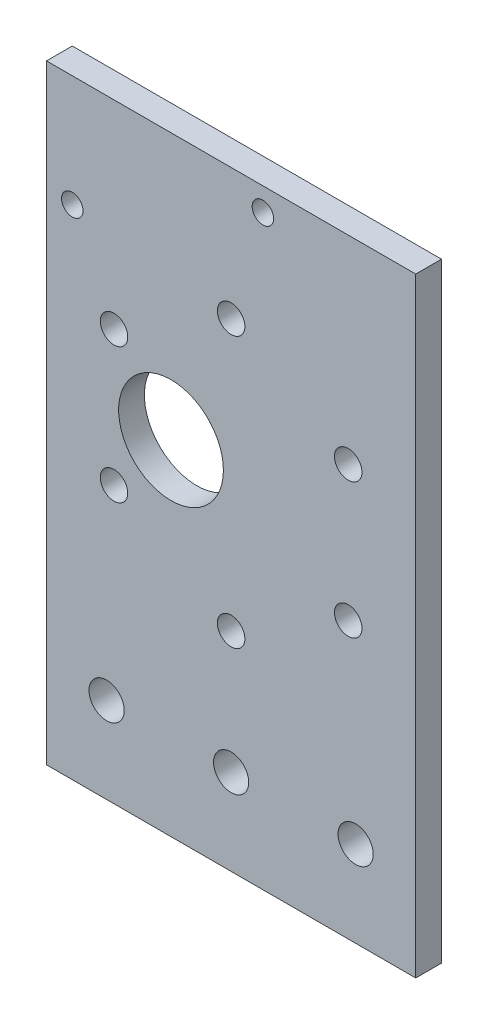
SolidWorks part; units mm, degrees
ref_plane "正面" through (0, 0, 0) normal (0, 0, 1) x (1, 0, 0)
ref_plane "平面" through (0, 0, 0) normal (0, 1, 0) x (1, 0, 0)
ref_plane "右側面" through (0, 0, 0) normal (1, 0, 0) x (0, 0, -1)
sketch "ｽｹｯﾁ1" plane through (0, 0, 0) normal (0, 0, 1) x (1, 0, 0)
  line L1 (-20, 14.5) -> (20, 14.5)
  line L2 (-20, 14.5) -> (-20, -14.5)
  line L3 (-20, -14.5) -> (20, -14.5)
  line L4 (20, 14.5) -> (20, -14.5)
  line L5 (-20, 14.5) -> (20, -14.5) construction
  line L6 (-20, -14.5) -> (20, 14.5) construction
  point P0 (0, 0)
  dimension "D1" = 40
  dimension "D2" = 29
extrude "ﾎﾞｽ - 押し出し1" add sketch "ｽｹｯﾁ1" along normal blind 3
sketch "ｽｹｯﾁ2" plane through (0, 0, 3) normal (0, 0, 1) x (1, 0, 0)
  line L1 (-20, 14.5) -> (-16.5, 14.5)
  line L2 (-20, 14.5) -> (-20, 10.5)
  line L3 (-20, 10.5) -> (-16.5, 10.5)
  line L4 (-16.5, 14.5) -> (-16.5, 10.5)
  line L5 (-20, -14.5) -> (-16.5, -14.5)
  line L6 (-20, -14.5) -> (-20, -10.5)
  line L7 (-20, -10.5) -> (-16.5, -10.5)
  line L8 (-16.5, -14.5) -> (-16.5, -10.5)
  line L9 (20, -14.5) -> (16.5, -14.5)
  line L10 (20, -14.5) -> (20, -10.5)
  line L11 (20, -10.5) -> (16.5, -10.5)
  line L12 (16.5, -14.5) -> (16.5, -10.5)
  line L13 (20, 14.5) -> (16.5, 14.5)
  line L14 (20, 14.5) -> (20, 10.5)
  line L15 (20, 10.5) -> (16.5, 10.5)
  line L16 (16.5, 14.5) -> (16.5, 10.5)
  circle A0 centre (-16.5, 10.5) radius 2.1
  circle A1 centre (-16.5, -10.5) radius 2.1
  circle A2 centre (16.5, -10.5) radius 2.1
  circle A3 centre (16.5, 10.5) radius 2.1
  dimension "D9" = 4.2
  dimension "D10" = 4.2
  dimension "D11" = 4.2
  dimension "D12" = 4.2
  dimension "D1" = 3.5
  dimension "D2" = 4
  dimension "D3" = 3.5
  dimension "D4" = 4
  dimension "D5" = 3.5
  dimension "D6" = 4
  dimension "D7" = 3.5
  dimension "D8" = 4
extrude "ｶｯﾄ - 押し出し1" cut sketch "ｽｹｯﾁ2" against normal blind 3 contours L3 A0 L4 | L4 A0 L3 | L8 A1 L7 | L7 A1 L8 | L12 A2 L11 | L11 A2 L12 | L16 A3 L15 | L15 A3 L16
sketch "ｽｹｯﾁ3" plane through (0, -14.5, 0) normal (0, -1, 0) x (1, 0, 0)
  line L1 (20, 0) -> (-20, 0)
  line L2 (20, 0) -> (20, 3)
  line L3 (20, 3) -> (-20, 3)
  line L4 (-20, 0) -> (-20, 3)
extrude "ﾎﾞｽ - 押し出し2" add sketch "ｽｹｯﾁ3" along normal blind 10
sketch "ｽｹｯﾁ4" plane through (0, 14.5, 0) normal (0, 1, 0) x (1, 0, 0)
  line L1 (20, -3) -> (-20, -3)
  line L2 (20, -3) -> (20, 0)
  line L3 (20, 0) -> (-20, 0)
  line L4 (-20, -3) -> (-20, 0)
extrude "ﾎﾞｽ - 押し出し3" add sketch "ｽｹｯﾁ4" along normal blind 10
sketch "ｽｹｯﾁ6" plane through (20, 0, 0) normal (1, 0, 0) x (0, 0, -1)
  line L1 (0, 24.5) -> (-3, 24.5)
  line L2 (0, 24.5) -> (0, -24.5)
  line L3 (0, -24.5) -> (-3, -24.5)
  line L4 (-3, 24.5) -> (-3, -24.5)
extrude "ﾎﾞｽ - 押し出し5" add sketch "ｽｹｯﾁ6" along normal blind 42
sketch "ｽｹｯﾁ7" plane through (0, 0, 3) normal (0, 0, 1) x (1, 0, 0)
  line L0 (62, 0) -> (43.1058, 0)
  line L1 (62, 24.5) -> (62, -24.5) construction
  line L2 (43.1058, 0) -> (36.1058, 0)
  line L7 (31.9689, -11.1369) -> (54.2427, 11.1369) construction
  line L8 (31.9689, 11.1369) -> (54.2427, -11.1369) construction
  line L9 (43.1058, 0) -> (29.4659, 7.875)
  line L10 (43.1058, 0) -> (43.1058, 15.75)
  line L11 (43.1058, 0) -> (56.7457, 7.875)
  line L12 (43.1058, 0) -> (29.4659, -7.875)
  line L13 (43.1058, 0) -> (43.1058, -15.75)
  line L14 (43.1058, 0) -> (56.7457, -7.875)
  circle A0 centre (43.1058, 0) radius 15.75
  circle A5 centre (29.4659, 7.875) radius 1.75
  circle A6 centre (43.1058, 15.75) radius 1.75
  circle A7 centre (29.4659, -7.875) radius 1.75
  circle A8 centre (43.1058, -15.75) radius 1.75
  circle A9 centre (56.7457, -7.875) radius 1.75
  circle A10 centre (56.7457, 7.875) radius 1.75
  circle A11 centre (36.1058, 0) radius 6.1
  dimension "D3" = 60
  dimension "D4" = 7
  dimension "D5" = 60
  dimension "D6" = 60
  dimension "D7" = 31.5
  dimension "D8" = 3.5
  dimension "D9" = 3.5
  dimension "D10" = 3.5
  dimension "D11" = 3.5
  dimension "D12" = 3.5
  dimension "D13" = 3.5
  dimension "D14" = 12.2
  dimension "D2" = 60
  dimension "D15" = 18.8942
sketch "ｽｹｯﾁ8" plane through (-20, 0, 0) normal (-1, 0, 0) x (0, 0, 1)
  line L1 (3, -24.5) -> (0, -24.5)
  line L2 (3, -24.5) -> (3, 24.5)
  line L3 (3, 24.5) -> (0, 24.5)
  line L4 (0, -24.5) -> (0, 24.5)
extrude "ﾎﾞｽ - 押し出し6" add sketch "ｽｹｯﾁ8" along normal blind 2
sketch "ｽｹｯﾁ9" plane through (62, 0, 0) normal (1, 0, 0) x (0, 0, -1)
  line L1 (0, 24.5) -> (-3, 24.5)
  line L2 (0, 24.5) -> (0, -24.5)
  line L3 (0, -24.5) -> (-3, -24.5)
  line L4 (-3, 24.5) -> (-3, -24.5)
extrude "ﾎﾞｽ - 押し出し7" add sketch "ｽｹｯﾁ9" along normal blind 2
sketch "ｽｹｯﾁ10" plane through (0, -24.5, 0) normal (0, -1, 0) x (1, 0, 0)
  line L1 (-22, 0) -> (64, 0)
  line L2 (-22, 0) -> (-22, 3)
  line L3 (-22, 3) -> (64, 3)
  line L4 (64, 0) -> (64, 3)
extrude "ﾎﾞｽ - 押し出し8" add sketch "ｽｹｯﾁ10" along normal blind 10
sketch "ｽｹｯﾁ11" plane through (0, 24.5, 0) normal (0, 1, 0) x (1, 0, 0)
  line L1 (-22, 0) -> (64, 0)
  line L2 (-22, 0) -> (-22, -3)
  line L3 (-22, -3) -> (64, -3)
  line L4 (64, 0) -> (64, -3)
extrude "ﾎﾞｽ - 押し出し9" add sketch "ｽｹｯﾁ11" along normal blind 10
sketch "ｽｹｯﾁ12" plane through (0, 0, 3) normal (0, 0, 1) x (1, 0, 0)
  line L0 (64, -34.5) -> (64, -27)
  line L1 (64, 34.5) -> (64, -34.5) construction
  line L2 (64, 34.5) -> (64, 27)
  line L3 (64, -27) -> (54, -27)
  line L4 (64, 27) -> (54, 27)
  line L5 (-22, -34.5) -> (-22, -27)
  line L6 (-22, -34.5) -> (-22, 34.5) construction
  line L7 (-22, 34.5) -> (-22, 27)
  line L8 (-22, -27) -> (-12, -27)
  line L9 (-22, 27) -> (-12, 27)
  circle A0 centre (54, -27) radius 2.2
  circle A1 centre (54, 27) radius 2.2
  circle A2 centre (-12, -27) radius 2.2
  circle A3 centre (-12, 27) radius 2.2
  dimension "D4" = 4.4
  dimension "D5" = 4.4
  dimension "D11" = 4.4
  dimension "D12" = 4.4
  dimension "D1" = 7.5
  dimension "D2" = 7.5
  dimension "D3" = 10
  dimension "D6" = 10
  dimension "D7" = 7.5
  dimension "D8" = 7.5
  dimension "D9" = 10
  dimension "D10" = 10
sketch "ｽｹｯﾁ14" plane through (-22, 0, 0) normal (-1, 0, 0) x (0, 0, 1)
  line L0 (0, 34.5) -> (0, -34.5) construction
  line L1 (3, -34.5) -> (0, -34.5)
  line L2 (3, -34.5) -> (3, 34.5)
  line L3 (3, 34.5) -> (0, 34.5)
  line L4 (0, -34.5) -> (0, 34.5)
  line L5 (0, 34.5) -> (3, 34.5) construction
extrude "ｶｯﾄ - 押し出し5" cut sketch "ｽｹｯﾁ14" against normal blind 43
sketch "ｽｹｯﾁ17" plane through (0, -34.5, 0) normal (0, -1, 0) x (1, 0, 0)
  line L1 (21, 3) -> (64, 3)
  line L2 (21, 3) -> (21, 0)
  line L3 (21, 0) -> (64, 0)
  line L4 (64, 3) -> (64, 0)
extrude "ﾎﾞｽ - 押し出し10" add sketch "ｽｹｯﾁ17" along normal blind 20
sketch "ｽｹｯﾁ18" plane through (0, 0, 3) normal (0, 0, 1) x (1, 0, 0)
  line L0 (21, -54.5) -> (21, -34.5)
  line L1 (21, -54.5) -> (21, 34.5) construction
  line L3 (64, -54.5) -> (64, -34.5)
  line L4 (64, 34.5) -> (64, -54.5) construction
  line L5 (64, -34.5) -> (57, -34.5)
  line L6 (21, -34.5) -> (28, -34.5)
  circle A0 centre (28, -34.5) radius 2.05
  circle A1 centre (57, -34.5) radius 2.05
  dimension "D5" = 4.1
  dimension "D6" = 4.1
  dimension "D1" = 20
  dimension "D2" = 20
  dimension "D3" = 7
  dimension "D4" = 7
extrude "ｶｯﾄ - 押し出し6" cut sketch "ｽｹｯﾁ18" against normal blind 10
sketch "ｽｹｯﾁ19" plane through (0, 0, 3) normal (0, 0, 1) x (1, 0, 0)
  line L0 (42.5, -54.5) -> (42.5, 34.5)
  line L1 (64, -54.5) -> (21, -54.5) construction
  line L2 (21, 34.5) -> (64, 34.5) construction
  circle A0 centre (28, -34.5) radius 2.05 construction
  circle A1 centre (57, -34.5) radius 2.05 construction
  dimension "D2" = 14.5
  dimension "D1" = 14.5
sketch "ｽｹｯﾁ20" plane through (0, -54.5, 0) normal (0, -1, 0) x (1, 0, 0)
  line L1 (64, 0) -> (21, 0)
  line L2 (64, 0) -> (64, 3)
  line L3 (64, 3) -> (21, 3)
  line L4 (21, 0) -> (21, 3)
extrude "ﾎﾞｽ - 押し出し11" add sketch "ｽｹｯﾁ20" along normal blind 10
sketch "ｽｹｯﾁ21" plane through (0, 34.5, 0) normal (0, 1, 0) x (1, 0, 0)
  line L1 (64, 0) -> (21, 0)
  line L2 (64, 0) -> (64, -3)
  line L3 (64, -3) -> (21, -3)
  line L4 (21, 0) -> (21, -3)
extrude "ｶｯﾄ - 押し出し7" cut sketch "ｽｹｯﾁ21" against normal blind 10
sketch "ｽｹｯﾁ22" plane through (0, 0, 3) normal (0, 0, 1) x (1, 0, 0)
  line L0 (28, -34.5) -> (28, -54.5)
  line L1 (57, -34.5) -> (57, -54.5)
  circle A0 centre (28, -54.5) radius 2.2
  circle A1 centre (57, -54.5) radius 2.2
  dimension "D2" = 4.4
  dimension "D4" = 4.4
  dimension "D1" = 20
  dimension "D3" = 20
sketch "ｽｹｯﾁ23" plane through (0, 0, 3) normal (0, 0, 1) x (1, 0, 0)
  line L0 (21, 24.5) -> (21, 22.0635)
  line L1 (21, -64.5) -> (21, 24.5) construction
  line L2 (21, 22.0635) -> (24.0484, 22.0635)
  line L3 (24.0484, 22.0635) -> (24.0484, 11.7635)
  line L4 (24.0484, 11.7635) -> (46.2484, 11.7635)
  dimension "D1" = 10.3
  dimension "D2" = 22.2
sketch "ｽｹｯﾁ24" plane through (0, 24.5, 0) normal (0, 1, 0) x (1, 0, 0)
  line L1 (21, 0) -> (64, 0)
  line L2 (21, 0) -> (21, -3)
  line L3 (21, -3) -> (64, -3)
  line L4 (64, 0) -> (64, -3)
extrude "ﾎﾞｽ - 押し出し12" add sketch "ｽｹｯﾁ24" along normal blind 10
sketch "ｽｹｯﾁ25" plane through (0, 0, 3) normal (0, 0, 1) x (1, 0, 0)
  line L0 (21, 34.5) -> (21, 31.5)
  line L1 (21, -64.5) -> (21, 34.5) construction
  line L2 (21, 31.5) -> (24, 31.5)
  line L3 (24, 31.5) -> (24, 13.5)
  line L4 (24, 13.5) -> (46.2, 13.5)
  line L5 (46.2, 13.5) -> (46.2, 23.8)
  circle A0 centre (24, 13.5) radius 1.55
  circle A1 centre (46.2, 23.8) radius 1.55
  dimension "D6" = 3.1
  dimension "D7" = 3.1
  dimension "D1" = 3
  dimension "D2" = 3
  dimension "D3" = 18
  dimension "D4" = 22.2
  dimension "D5" = 10.3
sketch "ｽｹｯﾁ28" plane through (0, 0, 3) normal (0, 0, 1) x (1, 0, 0)
  line L0 (64, 34.5) -> (42.5, 34.5)
  line L1 (21, 34.5) -> (64, 34.5) construction
  line L2 (42.5, 34.5) -> (42.5, -4.5)
  line L3 (42.5, -4.5) -> (35.5, -4.5)
  line L4 (42.5, -4.5) -> (28.8601, 3.375)
  line L5 (42.5, -4.5) -> (56.1399, 3.375)
  line L6 (42.5, -4.5) -> (56.1399, -12.375)
  line L7 (42.5, -4.5) -> (42.5, -20.25)
  line L8 (42.5, -4.5) -> (28.8601, -12.375)
  circle A0 centre (42.5, -4.5) radius 15.75
  circle A1 centre (35.5, -4.5) radius 6.1
  circle A2 centre (42.5, 11.25) radius 1.6
  circle A3 centre (28.8601, -12.375) radius 1.6
  circle A4 centre (28.8601, 3.375) radius 1.6
  circle A5 centre (56.1399, 3.375) radius 1.6
  circle A6 centre (56.1399, -12.375) radius 1.6
  circle A7 centre (42.5, -20.25) radius 1.6
  dimension "D2" = 31.5
  dimension "D4" = 12.2
  dimension "D9" = 3.2
  dimension "D10" = 3.2
  dimension "D11" = 3.2
  dimension "D12" = 3.2
  dimension "D13" = 3.2
  dimension "D14" = 3.2
  dimension "D1" = 21.5
  dimension "D3" = 7
  dimension "D5" = 60
  dimension "D6" = 60
  dimension "D7" = 60
  dimension "D8" = 60
  dimension "D15" = 39
extrude "ｶｯﾄ - 押し出し9" cut sketch "ｽｹｯﾁ28" against normal blind 10
sketch "ｽｹｯﾁ29" plane through (0, -64.5, 0) normal (0, -1, 0) x (-1, 0, 0)
  line L1 (-21, 0) -> (-64, 0)
  line L2 (-21, 0) -> (-21, -3)
  line L3 (-21, -3) -> (-64, -3)
  line L4 (-64, 0) -> (-64, -3)
extrude "ｶｯﾄ - 押し出し10" cut sketch "ｽｹｯﾁ29" against normal blind 20
sketch "ｽｹｯﾁ30" plane through (0, 0, 3) normal (0, 0, 1) x (1, 0, 0)
  line L1 (64, -44.5) -> (21, -44.5) construction
  line L3 (42.5, -34.5) -> (42.5, -44.5)
  circle A0 centre (42.5, -34.5) radius 2.05
  dimension "D2" = 4.1
  dimension "D1" = 10
extrude "ｶｯﾄ - 押し出し11" cut sketch "ｽｹｯﾁ30" against normal blind 10
hole_wizard "M3x0.5 ねじ穴1" positions "3Dｽｹｯﾁ1" profile "ｽｹｯﾁ31" tap size "M3x0.5" standard "JIS"
sketch3d "3Dｽｹｯﾁ1"
  point P0 (29.1712, -61.0225, 0)
  point P2 (46.2, 23.8, 3)
  point P5 (24, 13.5, 3)
sketch "ｽｹｯﾁ31" plane through (24, 13.5, 3) normal (1, 0, 0) x (0, -1, 0)
  line L0 (0, 0) -> (0, 9.2511)
  line L1 (0, 9.2511) -> (1.25, 8.5)
  line L2 (1.25, 8.5) -> (1.25, 0)
  line L5 (1.25, 0) -> (0, 0)
  line L10 (0, 9.2511) -> (-1.25, 8.5) construction
  line L11 (0, -6.35) -> (0, 107.95) construction
  dimension "ねじ下穴ﾄﾞﾘﾙ直径" = 2.5
  dimension "ねじ下穴ﾄﾞﾘﾙの深さ" = 8.5
  dimension "ﾄﾞﾘﾙ角度" = 118
cosmetic thread "穴のねじ山1" parameters "D1"=3, "D2"=3
cosmetic thread "穴のねじ山2" parameters "D1"=3, "D2"=3
cosmetic thread "穴のねじ山3" parameters "D1"=3, "D2"=3
sketch "ｽｹｯﾁ32" plane through (0, 34.5, 0) normal (0, 1, 0) x (1, 0, 0)
  line L1 (64, -3) -> (21, -3)
  line L2 (64, -3) -> (64, 0)
  line L3 (64, 0) -> (21, 0)
  line L4 (21, -3) -> (21, 0)
extrude "ｶｯﾄ - 押し出し12" cut sketch "ｽｹｯﾁ32" against normal blind 8
